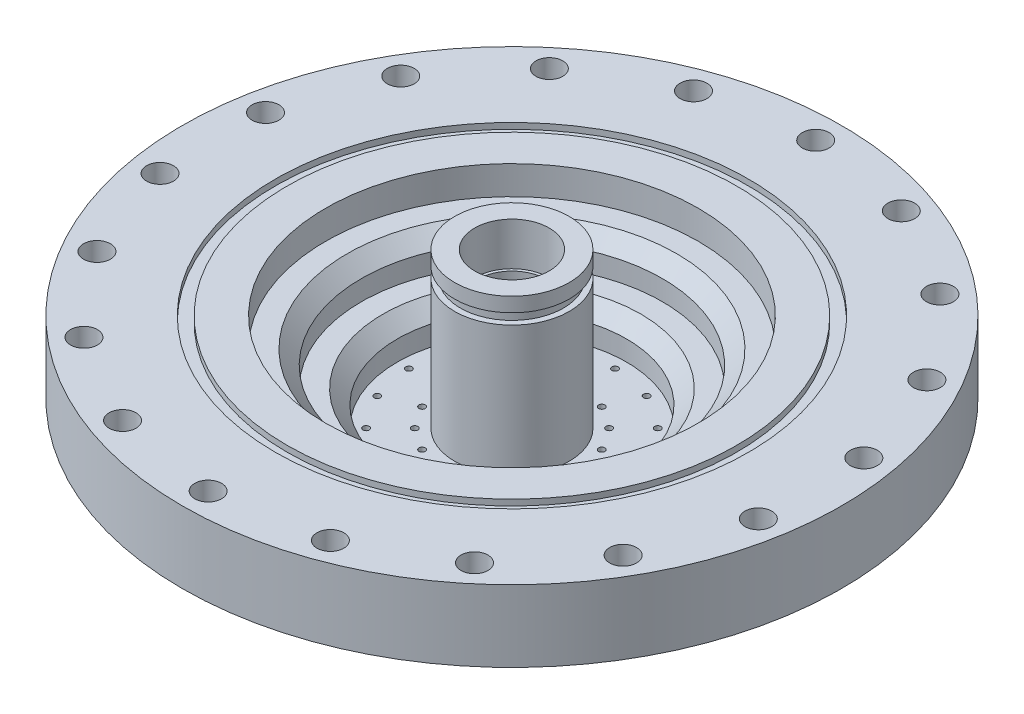
SolidWorks part; units mm, degrees
material "6061-T4 (SS)"
ref_plane "Front Plane" through (0, 0, 0) normal (0, 0, 1) x (1, 0, 0)
ref_plane "Top Plane" through (0, 0, 0) normal (0, 1, 0) x (1, 0, 0)
ref_plane "Right Plane" through (0, 0, 0) normal (1, 0, 0) x (0, 0, -1)
sketch "Sketch1" plane through (0, 0, 0) normal (0, 1, 0) x (1, 0, 0)
  circle A0 centre (0, 0) radius 38.1
  dimension "D1" = 76.2
extrude "Boss-Extrude1" add sketch "Sketch1" along normal blind 4.445
sketch "Sketch2" plane through (0, 4.445, 0) normal (0, 1, 0) x (1, 0, 0)
  circle A0 centre (0, 0) radius 28.575
  circle A1 centre (0, 0) radius 7.62
  dimension "D1" = 57.15
  dimension "D2" = 15.24
extrude "Boss-Extrude2" add sketch "Sketch2" along normal blind 5.08
sketch "Sketch4" plane through (0, 9.525, 0) normal (0, 1, 0) x (1, 0, 0)
  circle A0 centre (0, 0) radius 38.1
  circle A1 centre (0, 0) radius 7.62
  circle A2 centre (0, 0) radius 7.62 construction
  dimension "D1" = 76.2
extrude "Boss-Extrude3" add sketch "Sketch4" along normal blind 25.4
sketch "Sketch5" plane through (0, 34.925, 0) normal (0, 1, 0) x (1, 0, 0)
  circle A0 centre (0, 0) radius 73.025
  circle A1 centre (0, 0) radius 38.1
  circle A2 centre (0, 0) radius 38.1 construction
  dimension "D1" = 146.05
extrude "Boss-Extrude4" add sketch "Sketch5" against normal blind 19.05
sketch "Sketch6" plane through (0, 34.925, 0) normal (0, 1, 0) x (1, 0, 0)
  circle A0 centre (0, 0) radius 41.275
  circle A1 centre (0, 0) radius 12.7
  dimension "D1" = 25.4
  dimension "D2" = 82.55
extrude "Cut-Extrude1" cut sketch "Sketch6" against normal blind 9.525
sketch "Sketch7" plane through (0, 25.4, 0) normal (0, 1, 0) x (1, 0, 0)
  circle A0 centre (0, 0) radius 12.7
  circle A1 centre (0, 0) radius 33.3375
  circle A2 centre (0, 0) radius 12.7 construction
  dimension "D1" = 66.675
extrude "Cut-Extrude2" cut sketch "Sketch7" against normal blind 7.62
sketch "Sketch8" plane through (0, 17.78, 0) normal (0, 1, 0) x (1, 0, 0)
  circle A0 centre (0, 0) radius 12.7
  circle A1 centre (0, 0) radius 25.4
  circle A2 centre (0, 0) radius 12.7 construction
  dimension "D1" = 50.8
extrude "Cut-Extrude3" cut sketch "Sketch8" against normal blind 7.62
sketch "Sketch9" plane through (0, 0, 0) normal (0, 0, 1) x (1, 0, 0)
  line L0 (0, 0) -> (0, 34.925) construction
  line L1 (7.62, 34.925) -> (-7.62, 34.925) construction
  line L2 (7.62, 4.445) -> (-7.62, 4.445) construction
  circle A0 centre (0, 6.985) radius 1.5875
  dimension "D2" = 3.175
  dimension "D1" = 2.54
sketch "Sketch10" plane through (0, 34.925, 0) normal (0, 1, 0) x (1, 0, 0)
  circle A0 centre (0, 0) radius 12.7
  circle A1 centre (0, 0) radius 8.255
  circle A3 centre (0, 0) radius 12.7 construction
  dimension "D1" = 16.51
extrude "Boss-Extrude5" add sketch "Sketch10" along normal blind 9.525
sketch "Sketch11" plane through (0, 0, 0) normal (0, 0, 1) x (1, 0, 0)
  line L0 (0, 0) -> (-38.0746, 0) construction
  line L1 (-38.1, 0) -> (38.1, 0) construction
  line L2 (-38.0746, 0) -> (-38.0746, 4.445) construction
  line L3 (38.1, 4.445) -> (-38.1, 4.445) construction
  line L4 (-38.0746, 2.2225) -> (-36.83, 2.2225) construction
  line L5 (-36.83, 3.4036) -> (-36.83, 1.0414)
  line L6 (-36.83, 3.4036) -> (-38.0746, 3.4036)
  line L7 (-36.83, 1.0414) -> (-38.0746, 1.0414)
  line L8 (-38.0746, 3.4036) -> (-38.0746, 1.0414)
  line L9 (0, 0) -> (0, 24.1447) construction
  point P10 (-36.83, 2.2225)
  dimension "D1" = 38.0746
  dimension "D2" = 36.83
  dimension "D3" = 2.3622
chamfer "Chamfer1" distance 3.175 angle 45 2 edges at (0, 17.78, 25.4) (0, 25.4, 33.3375)
sketch "Sketch12" plane through (0, 0, 0) normal (0, -1, 0) x (1, 0, 0)
  line L0 (0, 0) -> (0, 38.1) construction
  line L1 (0, 0) -> (14.5705, 35.1763) construction
  line L2 (14.5705, 35.1763) -> (11.6564, 28.1411) construction
  line L3 (11.6564, 28.1411) -> (8.7423, 21.1058) construction
  line L4 (8.7423, 21.1058) -> (5.8282, 14.0705) construction
  line L5 (5.8282, 14.0705) -> (2.9141, 7.0353) construction
  line L6 (2.9141, 7.0353) -> (0, 0) construction
  circle A0 centre (0, 0) radius 38.1 construction
  circle A1 centre (5.8282, 14.0705) radius 0.6985
  circle A2 centre (8.7423, 21.1058) radius 0.6985
  dimension "D2" = 1.397
  dimension "D1" = 22.5
  dimension "D3" = 38.0746
extrude "Cut-Extrude5" cut sketch "Sketch12" against normal up to next (10.16 mm away)
ref_plane "Plane1" through (0, 0, 0) normal (-0.9239, 0, 0.3827) x (0.3827, 0, 0.9239)
sketch "Sketch13" plane through (0, 0, 0) normal (-0.9239, 0, 0.3827) x (0.3827, 0, 0.9239)
  line L0 (7.6149, 0) -> (4.4269, 5.5217)
  line L1 (30.4597, 0) -> (34.3765, 6.7842)
  line L2 (0, 0) -> (38.0746, 0) construction
  line L3 (30.4597, 0) -> (22.8448, 0) construction
  line L4 (30.4597, 0) -> (26.107, -7.539) construction
  line L5 (7.6149, 0) -> (11.9676, -7.539)
  line L6 (22.5375, -1.4364) -> (1.3976, -13.6416) construction
  line L7 (37.4085, -14.0639) -> (14.8055, -1.0141) construction
  point P15 (11.9676, -7.539)
  point P18 (26.107, -7.539)
  dimension "D1" = 60
  dimension "D2" = 60
ref_plane "Plane2" through (2.3942, -10.8364, 5.7801) normal (-0.1913, 0.866, -0.4619) x (-0.3314, -0.5, -0.8001)
sketch "Sketch14" plane through (2.3942, -10.8364, 5.7801) normal (-0.1913, 0.866, -0.4619) x (-0.3314, -0.5, -0.8001)
  circle A0 centre (-6.5947, 0) radius 0.508
  dimension "D1" = 1.016
extrude "Cut-Extrude6" cut sketch "Sketch14" along normal up to next
ref_plane "Plane3" through (1.2484, 5.6504, 3.014) normal (0.1913, 0.866, 0.4619) x (-0.3314, 0.5, -0.8001)
sketch "Sketch15" plane through (1.2484, 5.6504, 3.014) normal (0.1913, 0.866, 0.4619) x (-0.3314, 0.5, -0.8001)
  circle A0 centre (-26.3789, 0) radius 0.508
  dimension "D1" = 1.016
extrude "Cut-Extrude7" cut sketch "Sketch15" along normal up to next
pattern_circular "CirPattern2" count 16 over 360 about axis through (0, 0, 0) along (0, 1, 0) of "Cut-Extrude5", "Cut-Extrude6", "Cut-Extrude7"
sketch "Sketch16" plane through (0, 0, 0) normal (0, 0, 1) x (1, 0, 0)
  line L0 (0, 0) -> (0, 44.45) construction
  line L1 (-38.1, 0) -> (38.1, 0) construction
  line L2 (8.255, 44.45) -> (-8.255, 44.45) construction
  line L3 (0, 44.45) -> (-12.7, 44.45) construction
  line L4 (12.7, 44.45) -> (-12.7, 44.45) construction
  line L9 (-12.7, 44.45) -> (-12.7, 41.275) construction
  line L11 (-12.7, 41.275) -> (-11.43, 41.275)
  line L12 (-12.7, 41.275) -> (-12.7, 38.9128)
  line L13 (-12.7, 38.9128) -> (-11.43, 38.9128)
  line L14 (-11.43, 41.275) -> (-11.43, 38.9128)
  dimension "D1" = 12.7
  dimension "D2" = 3.175
  dimension "D3" = 22.86
  dimension "D4" = 2.3622
revolve "Cut-Revolve2" cut sketch "Sketch16" angle 360 about L0
sketch "Sketch17" plane through (0, 34.925, 0) normal (0, 1, 0) x (1, 0, 0)
  circle A0 centre (0, 0) radius 67.31 construction
  circle A1 centre (0, 67.31) radius 2.9769
  dimension "D1" = 134.62
  dimension "D2" = 5.9538
extrude "Cut-Extrude8" cut sketch "Sketch17" against normal through all
pattern_circular "CirPattern3" count 18 over 360 about axis through (0, 0, 0) along (0, 1, 0) of "Cut-Extrude8"
sketch "Sketch20" plane through (0, 34.925, 0) normal (0, 1, 0) x (1, 0, 0)
  circle A0 centre (0, 0) radius 86.431
  circle A1 centre (0, 0) radius 37.2213
extrude "Cut-Extrude11" cut sketch "Sketch20" against normal blind 3.175
sketch "Sketch18" plane through (0, 31.75, 0) normal (0, 1, 0) x (1, 0, 0)
  circle A0 centre (0, 0) radius 49.7967
  circle A1 centre (0, 0) radius 52.4383
  circle A3 centre (0, 0) radius 41.275 construction
  dimension "D1" = 2.6416
  dimension "D2" = 104.8766
extrude "Cut-Extrude9" cut sketch "Sketch18" against normal blind 1.3208
ref_plane "Plane4" through (0, 0, 0) normal (0.9808, 0, -0.1951) x (0, 1, 0)
sketch "Sketch19" plane through (0, 0, 0) normal (0.9808, 0, -0.1951) x (0, 1, 0)
  line L0 (0, 0) -> (9.8103, 0) construction
  circle A0 centre (6.35, 0) radius 0.7938
  dimension "D1" = 1.5875
  dimension "D2" = 6.35
extrude "Cut-Extrude10" cut sketch "Sketch19" against normal through all
pattern_circular "CirPattern4" count 16 over 360 about axis through (0, 15.875, 0) along (0, 1, 0) of "Cut-Extrude10"
sketch "Sketch21" plane through (0, 0, 0) normal (0, 0, 1) x (1, 0, 0)
  line L0 (0, 0) -> (0, 49.8913) construction
  line L1 (0, 0) -> (38.0746, 0) construction
  line L2 (-38.1, 0) -> (38.1, 0) construction
  line L3 (38.0746, 0) -> (38.0746, 4.445) construction
  line L4 (38.1, 4.445) -> (-38.1, 4.445) construction
  line L6 (39.3192, 3.4036) -> (36.83, 3.4036)
  line L7 (39.3192, 3.4036) -> (39.3192, 1.0414)
  line L8 (39.3192, 1.0414) -> (36.83, 1.0414)
  line L9 (36.83, 3.4036) -> (36.83, 1.0414)
  line L10 (39.3192, 3.4036) -> (36.83, 1.0414) construction
  line L11 (39.3192, 1.0414) -> (36.83, 3.4036) construction
  point P9 (38.0746, 2.2225)
  dimension "D1" = 76.1492
  dimension "D2" = 73.66
  dimension "D3" = 2.3622
revolve "Cut-Revolve3" cut sketch "Sketch21" angle 360 about L0
